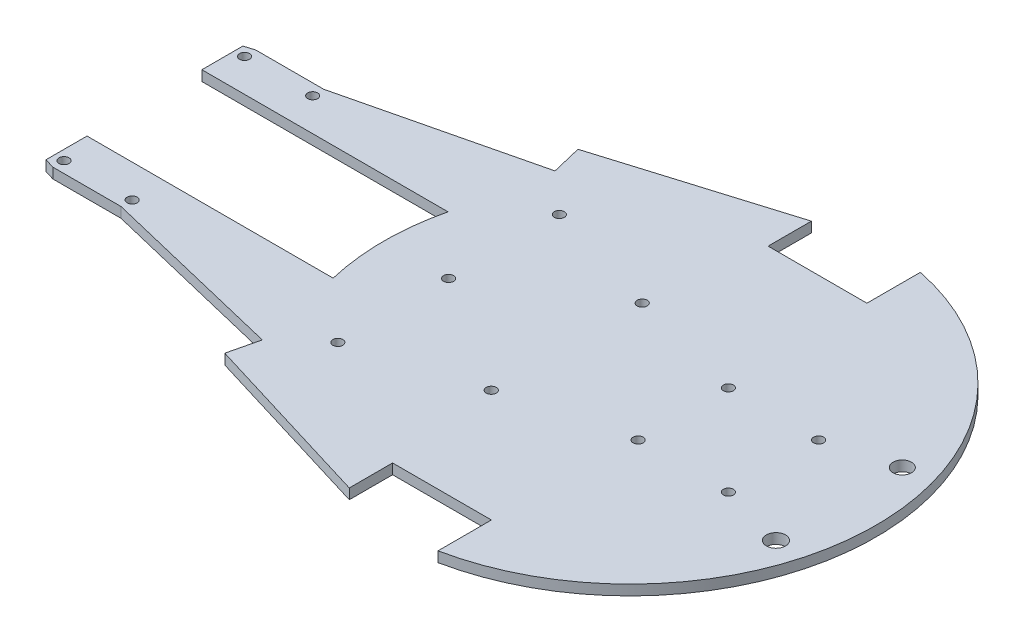
SolidWorks part; units mm, degrees
material "Acrylic (Medium-high impact)"
ref_plane "Front Plane" through (0, 0, 0) normal (0, 0, 1) x (1, 0, 0)
ref_plane "Top Plane" through (0, 0, 0) normal (0, 1, 0) x (1, 0, 0)
ref_plane "Right Plane" through (0, 0, 0) normal (1, 0, 0) x (0, 0, -1)
sketch "Sketch1" plane through (0, 0, 0) normal (0, 1, 0) x (1, 0, 0)
  line L0 (-276.2286, 0) -> (243.9296, 0) construction
  line L1 (-74.0966, 17.78) -> (-150.2966, 17.78)
  line L2 (-150.2966, 17.78) -> (-150.2966, 30.48)
  line L3 (-150.2966, 30.48) -> (0, 76.2)
  line L4 (-74.0966, -17.78) -> (-150.2966, -17.78)
  line L5 (-150.2966, -17.78) -> (-150.2966, -30.48)
  line L6 (-150.2966, -30.48) -> (0, -76.2)
  line L7 (0, 0) -> (0, 119.7586) construction
  line L8 (-74.0966, 17.78) -> (0, 76.2)
  line L9 (-74.0966, -17.78) -> (0, -76.2)
  line L10 (-15.3523, 74.6374) -> (-15.3523, 58.1274)
  line L11 (-15.3523, 58.1274) -> (15.24, 58.1274)
  line L12 (15.24, 58.1274) -> (15.24, 74.6604)
  line L13 (-15.3523, -74.6374) -> (-15.3523, -58.1274)
  line L14 (15.24, -58.1274) -> (15.24, -74.6604)
  line L15 (-15.3523, -58.1274) -> (15.24, -58.1274)
  line L16 (44.45, 13.97) -> (44.45, -19.0747) construction
  line L19 (-114.3908, 41.4025) -> (-135.6446, 34.9371)
  line L20 (-147.2486, 31.4072) -> (-126.1666, 31.4072)
  line L21 (-126.1666, 31.4072) -> (-126.1666, 37.8203)
  line L22 (-126.1666, 37.8203) -> (-147.2486, 31.4072)
  line L23 (-126.1666, -31.4072) -> (-126.1666, -37.8203)
  line L24 (-147.2486, -31.4072) -> (-126.1666, -31.4072)
  line L25 (-147.2486, -31.4072) -> (-126.1666, -37.8203)
  line L26 (-56.1402, 0) -> (-19.5642, 0)
  line L27 (-19.5642, 16.0868) -> (-19.5642, -25.7502) construction
  line L28 (-19.5642, 0) -> (-19.5642, 23.368)
  circle A0 centre (0, 0) radius 76.2
  arc A1 (-15.3523, 74.6374) -> (15.24, 74.6604) centre (0, 0) ccw
  circle A2 centre (44.45, 13.97) radius 1.55
  circle A4 centre (16.51, -13.97) radius 1.55
  circle A5 centre (16.51, 13.97) radius 1.55
  circle A6 centre (44.45, -13.97) radius 1.55
  circle A7 centre (64.77, 19.558) radius 2.8541
  circle A8 centre (64.77, -19.558) radius 2.9733
  circle A9 centre (-147.2486, 27.94) radius 1.55
  circle A10 centre (-126.1666, 27.94) radius 1.55
  circle A11 centre (-147.2486, -27.94) radius 1.55
  circle A12 centre (-126.1666, -27.94) radius 1.55
  circle A18 centre (-56.1402, 0) radius 1.55
  circle A19 centre (-56.1402, 34.29) radius 1.55
  circle A20 centre (-56.1402, -34.29) radius 1.55
  circle A23 centre (-19.5642, 23.368) radius 1.55
  circle A24 centre (-19.5642, -23.368) radius 1.55
  dimension "D1" = 152.4
  dimension "D8" = 3.1
  dimension "D9" = 3.1
  dimension "D10" = 27.94
  dimension "D11" = 3.1
  dimension "D15" = 13.97
  dimension "D17" = 44.45
  dimension "D21" = 3.1
  dimension "D23" = 21.082
  dimension "D25" = 3.1
  dimension "D26" = 34.29
  dimension "D27" = 34.29
  dimension "D30" = 3.1
  dimension "D2" = 76.2
  dimension "D3" = 12.7
  dimension "D4" = 17.78
  dimension "D5" = 15.3523
  dimension "D6" = 15.24
  dimension "D7" = 16.51
  dimension "D12" = 27.94
  dimension "D13" = 27.94
  dimension "D14" = 27.94
  dimension "D16" = 13.97
  dimension "D18" = 19.558
  dimension "D19" = 39.116
  dimension "D20" = 64.77
  dimension "D22" = 3.048
  dimension "D24" = 2.54
  dimension "D28" = 36.576
  dimension "D29" = 23.368
extrude "Boss-Extrude1" add sketch "Sketch1" along normal blind 3.175
sketch "Sketch2" plane through (0, 3.175, 0) normal (0, 1, 0) x (1, 0, 0)
  line L0 (-15.3523, 58.1274) -> (-126.1666, 31.4072)
  line L1 (-126.1666, 31.4072) -> (-126.1666, 37.8203)
  line L2 (-126.1666, 37.8203) -> (-70.7595, 54.6751)
  line L3 (-126.1666, 37.8203) -> (-15.3523, 71.5298) construction
  line L4 (-70.7595, 54.6751) -> (-68.5017, 45.3117)
  line L5 (0, 0) -> (-167.7968, 0) construction
  line L6 (-126.1666, -31.4072) -> (-126.1666, -37.8203)
  line L7 (-126.1666, -37.8203) -> (-70.7595, -54.6751)
  line L8 (-70.7595, -54.6751) -> (-68.5017, -45.3117)
  line L9 (-15.3523, -58.1274) -> (-126.1666, -31.4072)
  line M14 (-126.1666, -31.4072) -> (-126.1666, -37.8203)
  line M15 (-126.1666, -37.8203) -> (-15.3523, -71.5298)
  line M23 (-15.3523, 71.5298) -> (-126.1666, 37.8203)
  line M24 (-126.1666, 37.8203) -> (-126.1666, 31.4072)
extrude "Cut-Extrude1" cut sketch "Sketch2" against normal up to surface (3.175 mm away) contours L4 L0 M23 M24 | L8 L9 M14 M15 up to face at (-126.1666, 0, -26.39)
